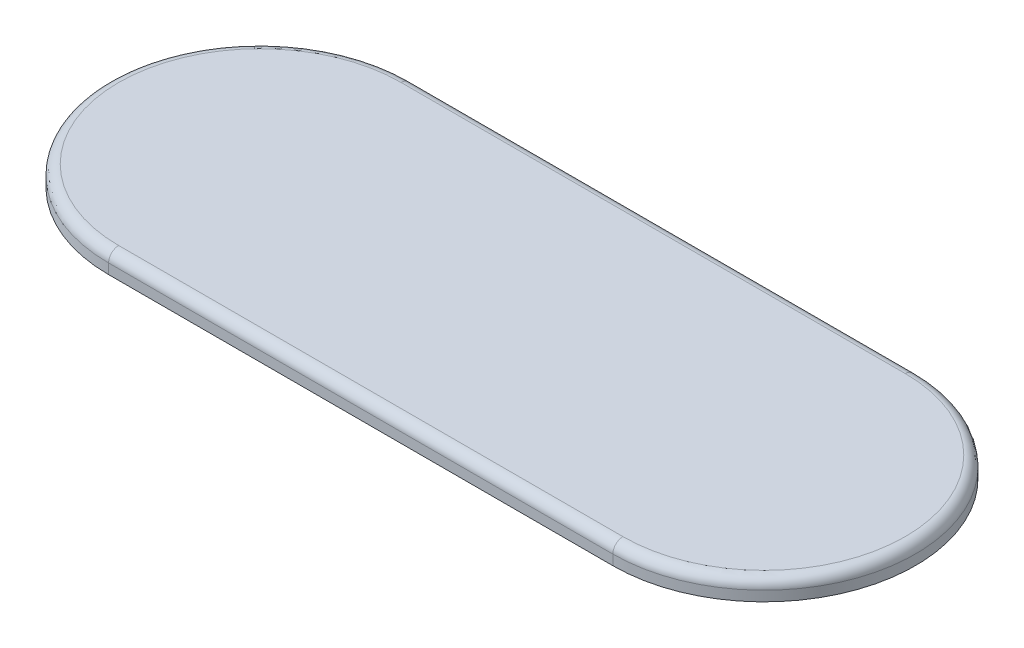
SolidWorks part; units mm, degrees
ref_plane "Front Plane" through (0, 0, 0) normal (0, 0, 1) x (1, 0, 0)
ref_plane "Top Plane" through (0, 0, 0) normal (0, 1, 0) x (1, 0, 0)
ref_plane "Right Plane" through (0, 0, 0) normal (1, 0, 0) x (0, 0, -1)
sketch "Sketch1" plane through (0, 0, 0) normal (0, 1, 0) x (1, 0, 0)
  line L0 (0, 0) -> (50, 0) construction
  line L1 (0, 15) -> (50, 15)
  line L2 (0, -15) -> (50, -15)
  arc A0 (0, 15) -> (0, -15) centre (0, 0) ccw
  arc A1 (50, -15) -> (50, 15) centre (50, 0) ccw
  point P3 (25, 0)
extrude "Boss-Extrude1" add sketch "Sketch1" along normal blind 2 contours L2 A1 L1 A0
fillet "Fillet1" radius 1 4 edges at (25, 2, -15) (65, 2, 0) (25, 2, 15) (-15, 2, 0)
